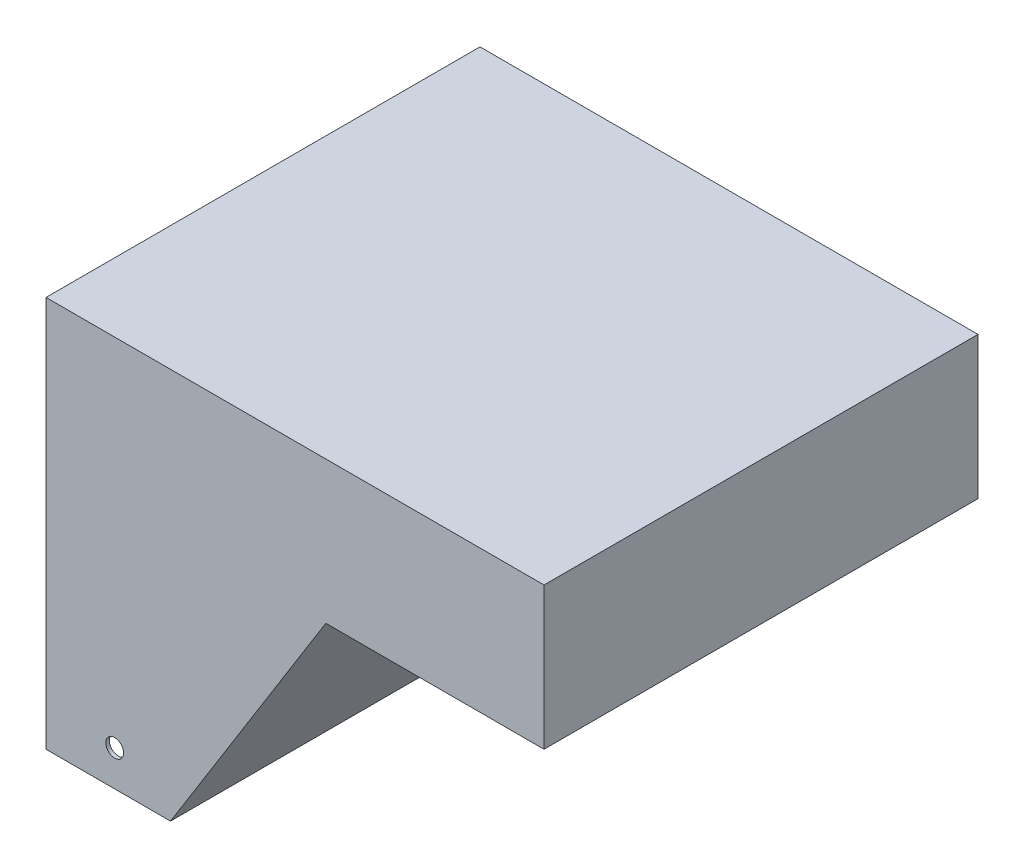
SolidWorks part; units mm, degrees
material "Acrylic (Medium-high impact)"
ref_plane "Front Plane" through (0, 0, 0) normal (0, 0, 1) x (1, 0, 0)
ref_plane "Top Plane" through (0, 0, 0) normal (0, 1, 0) x (1, 0, 0)
ref_plane "Right Plane" through (0, 0, 0) normal (1, 0, 0) x (0, 0, -1)
sketch "Sketch2" plane through (0, 0, 0) normal (0, 0, 1) x (1, 0, 0)
  line L0 (0, 0) -> (355.6, 0)
  line L1 (355.6, 0) -> (355.6, -101.6)
  line L2 (355.6, -101.6) -> (199.8078, -101.6)
  line L3 (199.8078, -101.6) -> (88.9, -279.4)
  line L4 (88.9, -279.4) -> (0, -279.4)
  line L5 (0, -279.4) -> (0, 0)
  circle A0 centre (49.0381, -254) radius 6.35
  dimension "D6" = 12.7
  dimension "D1" = 355.6
  dimension "D2" = 279.4
  dimension "D3" = 101.6
  dimension "D4" = 88.9
  dimension "D5" = 25.4
extrude "Boss-Extrude1" add sketch "Sketch2" along normal blind 2.54
sketch "Sketch3" plane through (0, 0, 2.54) normal (0, 0, 1) x (1, 0, 0)
  line L6 (2.54, -276.86) -> (2.54, -279.4)
  line L7 (0, -279.4) -> (88.9, -279.4) construction
  line L8 (87.4908, -276.86) -> (87.4908, -279.4)
  line L12 (2.54, -2.54) -> (2.54, -276.86)
  line L13 (2.54, -276.86) -> (87.4908, -276.86)
  line L14 (87.4908, -276.86) -> (198.3986, -99.06)
  line L15 (198.3986, -99.06) -> (353.06, -99.06)
  line L16 (353.06, -99.06) -> (353.06, -2.54)
  line L17 (353.06, -2.54) -> (2.54, -2.54)
  line L18 (2.54, -2.54) -> (2.54, -276.86)
  line L20 (87.4908, -276.86) -> (198.3986, -99.06)
  line L21 (198.3986, -99.06) -> (353.06, -99.06)
  line L22 (353.06, -99.06) -> (353.06, -2.54)
  line L23 (353.06, -2.54) -> (2.54, -2.54)
  dimension "D1" = 2.54
extrude "Boss-Extrude2" add sketch "Sketch3" along normal blind 304.8
ref_plane "Plane1" through (0, 0, 154.94) normal (0, 0, 1) x (1, 0, 0)
mirror "Mirror1" about plane through (0, 0, 154.94) normal (0, 0, 1) of "Boss-Extrude1"
